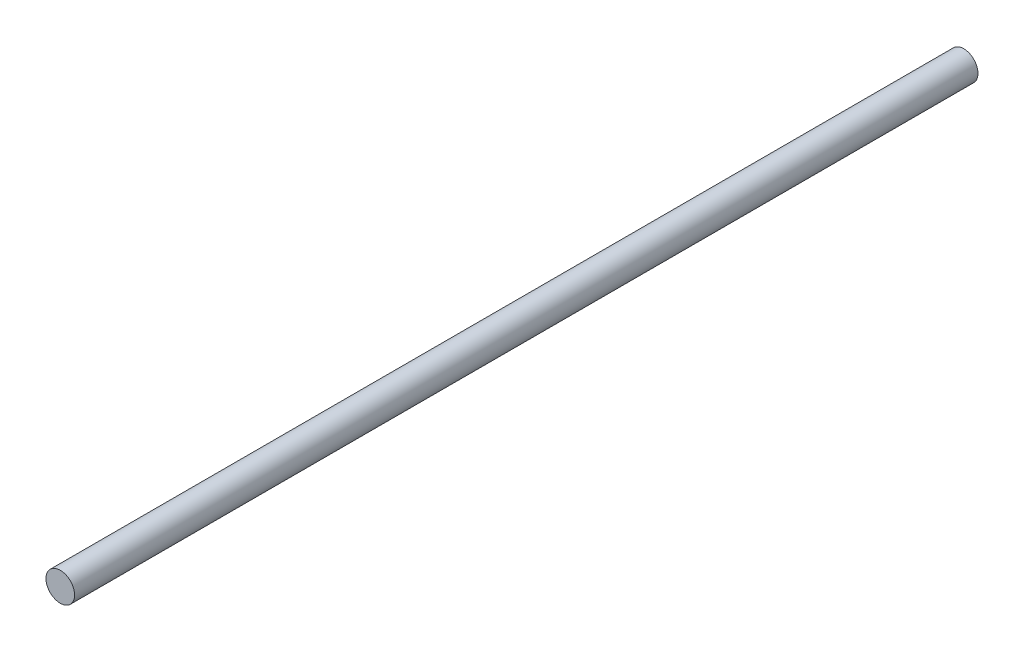
SolidWorks part; units mm, degrees
material "6061-T6 (SS)"
ref_plane "Front Plane" through (0, 0, 0) normal (0, 0, 1) x (1, 0, 0)
ref_plane "Top Plane" through (0, 0, 0) normal (0, 1, 0) x (1, 0, 0)
ref_plane "Right Plane" through (0, 0, 0) normal (1, 0, 0) x (0, 0, -1)
sketch "Sketch1" plane through (0, 0, 0) normal (0, 0, 1) x (1, 0, 0)
  circle A0 centre (0, 0) radius 2.413
  dimension "D1" = 4.826
extrude "Boss-Extrude1" add sketch "Sketch1" along normal blind 152.4
